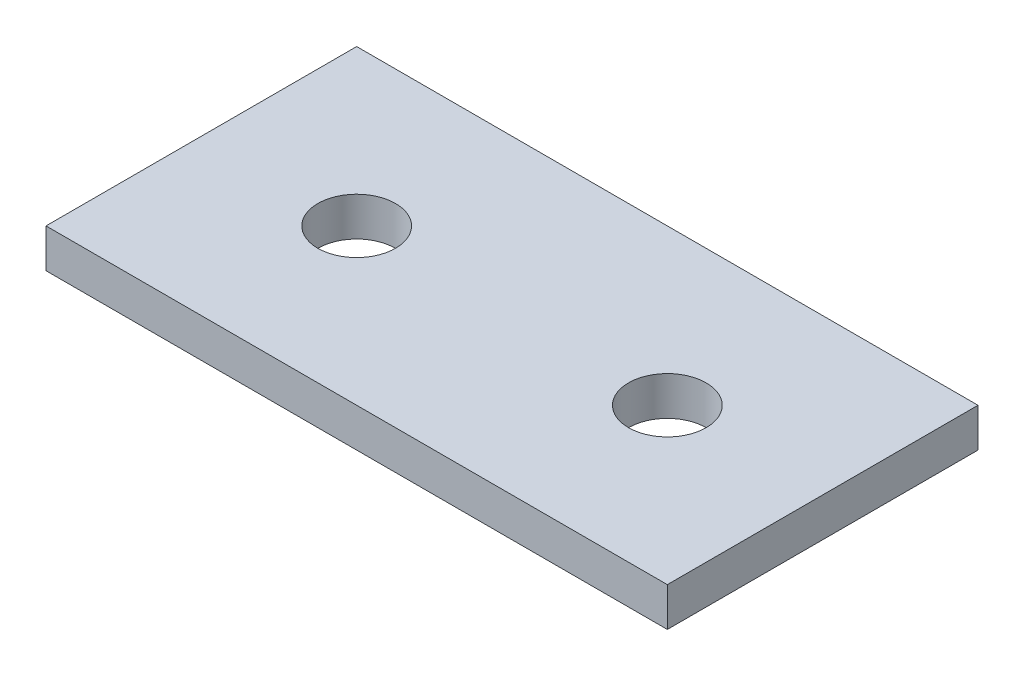
SolidWorks part; units mm, degrees
ref_plane "Front Plane" through (0, 0, 0) normal (0, 0, 1) x (1, 0, 0)
ref_plane "Top Plane" through (0, 0, 0) normal (0, 1, 0) x (1, 0, 0)
ref_plane "Right Plane" through (0, 0, 0) normal (1, 0, 0) x (0, 0, -1)
sketch "Sketch1" plane through (0, 0, 0) normal (0, 1, 0) x (1, 0, 0)
  line L0 (0, 12.7) -> (12.7, 12.7) construction
  line L1 (0, 0) -> (50.8, 0)
  line L2 (0, 0) -> (0, 25.4)
  line L3 (0, 25.4) -> (50.8, 25.4)
  line L4 (50.8, 0) -> (50.8, 25.4)
  line L5 (12.7, 12.7) -> (38.1, 12.7) construction
  line L6 (38.1, 12.7) -> (50.8, 12.7) construction
  circle A0 centre (12.7, 12.7) radius 3.175
  circle A1 centre (38.1, 12.7) radius 3.175
  dimension "D4" = 6.35
  dimension "D1" = 50.8
  dimension "D2" = 25.4
  dimension "D3" = 25.4
extrude "Boss-Extrude1" add sketch "Sketch1" along normal blind 3.175
